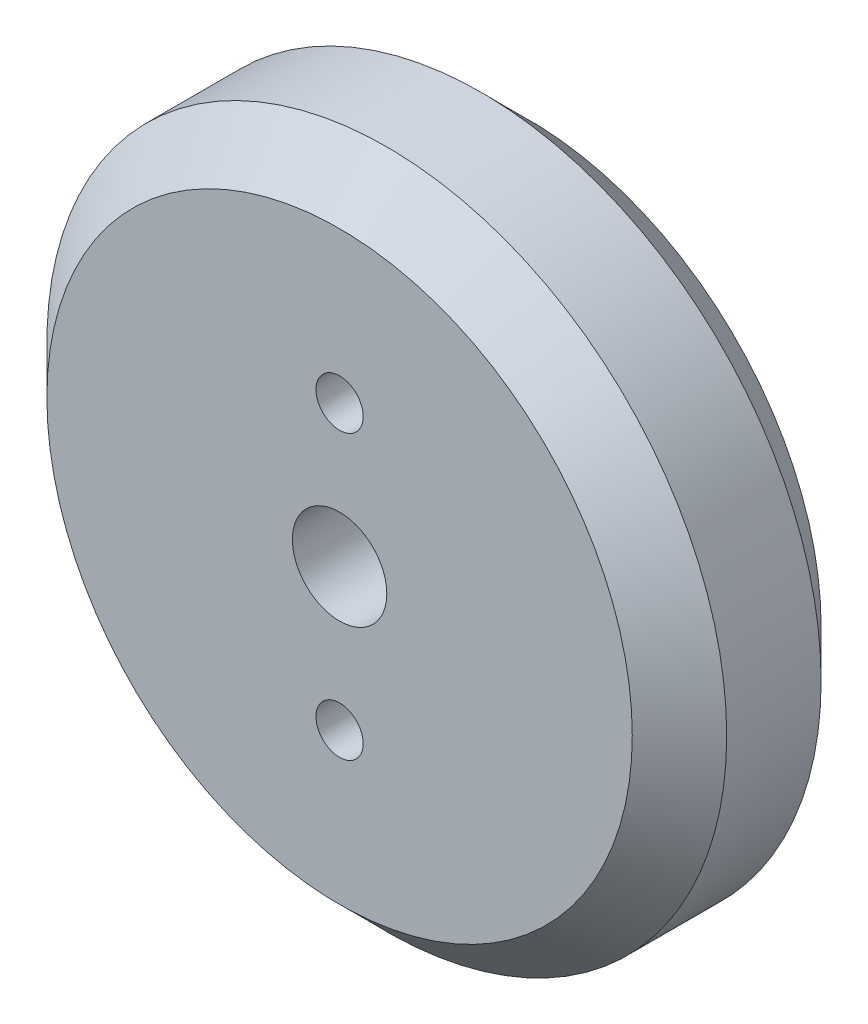
SolidWorks part; units mm, degrees
ref_plane "前基準面" through (0, 0, 0) normal (0, 0, 1) x (1, 0, 0)
ref_plane "上基準面" through (0, 0, 0) normal (0, 1, 0) x (1, 0, 0)
ref_plane "右基準面" through (0, 0, 0) normal (1, 0, 0) x (0, 0, -1)
sketch "草圖1" plane through (0, 0, 0) normal (0, 0, 1) x (1, 0, 0)
  line L0 (-20.9749, 0) -> (9.2062, 0) construction
  circle A0 centre (0, 0) radius 36
  circle A1 centre (0, 0) radius 5
  circle A2 centre (0, 15) radius 2.5
  circle A3 centre (0, -15) radius 2.5
  dimension "D1" = 72
  dimension "D2" = 10
  dimension "D3" = 5
  dimension "D4" = 15
extrude "填料-伸長1" add sketch "草圖1" along normal blind 20
chamfer "導角1" distance 5 angle 45 2 edges at (36, 0, 0) (36, 0, 20)
